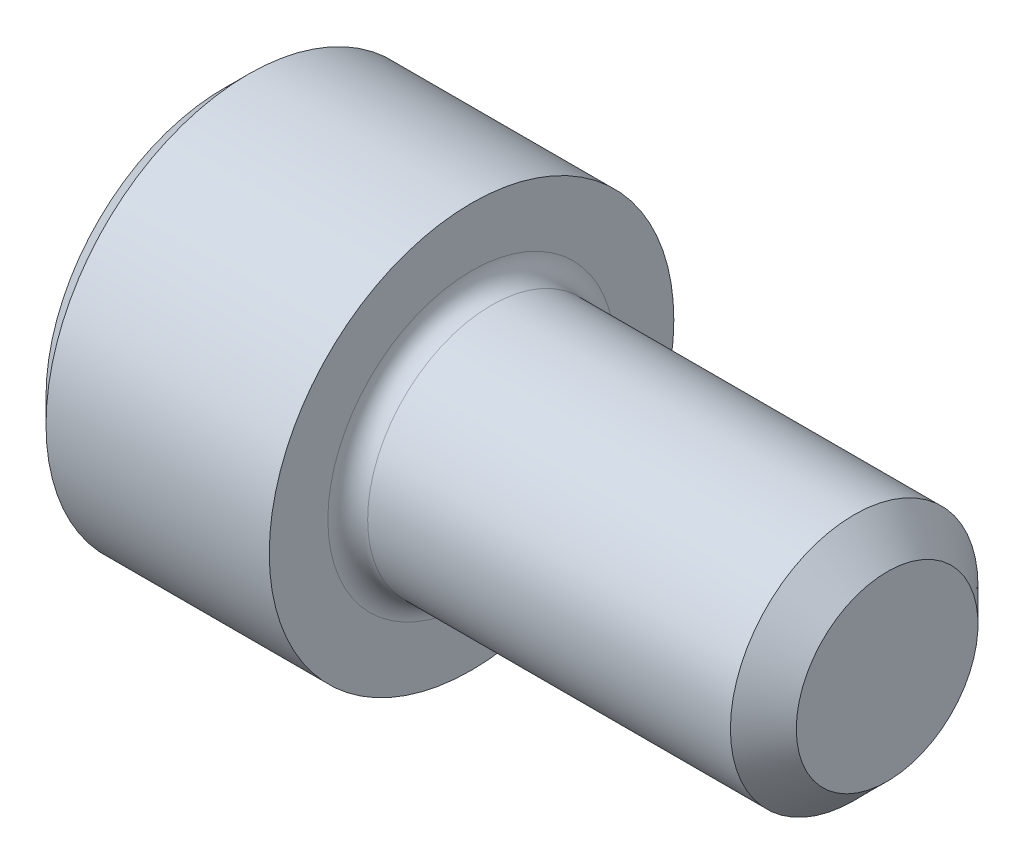
SolidWorks part; units mm, degrees
ref_plane "Plane1" through (0, 0, 0) normal (0, 0, 1) x (1, 0, 0)
ref_plane "Plane2" through (0, 0, 0) normal (0, 1, 0) x (1, 0, 0)
ref_plane "Plane3" through (0, 0, 0) normal (1, 0, 0) x (0, 0, -1)
sketch "BodySke" plane through (0, 0, 0) normal (0, 0, 1) x (1, 0, 0)
  line L0 (0, 0) -> (0, 2.0447)
  line L1 (0.2794, 2.3241) -> (2.8448, 2.3241)
  line L2 (2.8448, 2.3241) -> (2.8448, 1.4224)
  line L3 (2.8448, 1.4224) -> (7.2415, 1.4224)
  line L4 (7.62, 1.0439) -> (7.62, 0)
  line L5 (7.62, 0) -> (0, 0)
  line L6 (-31.75, 0) -> (127, 0) construction
  line L7 (0, 2.0447) -> (0.2794, 2.3241)
  line L8 (7.62, 1.0439) -> (7.2415, 1.4224)
  line L9 (0, -2.0447) -> (0.2794, -2.3241) construction
  line L10 (7.62, -1.0439) -> (7.2415, -1.4224) construction
  line L11 (3.4798, 9.525) -> (3.4798, 3.175) construction
  line L12 (2.8448, 9.525) -> (2.8448, 3.175) construction
  line L13 (-30.48, 9.525) -> (-30.48, 3.175) construction
  dimension "Diameter" = 2.8448
  dimension "Head_ht" = 2.8448
  dimension "Length" = 4.7752
  dimension "Body_ch_ang" = 45
  dimension "Head_dia" = 4.6482
  dimension "Head_ch_ang" = 45
  dimension "Head_side_ht" = 2.5654
  dimension "Minor_dia" = 2.0879
  dimension "Advance" = 0.635
  dimension "Thread_nom" = 4.7752
  dimension "Thread_length" = 38.1
revolve "Base-Revolve" add sketch "BodySke"
cosmetic thread "ThreadCosmetic" [suppressed]
fillet "Fillet1" radius 0.2286 1 edges at (2.8448, 0, 1.4224)
sketch "Sketch2" plane through (0, 0, 0) normal (0, 0, 1) x (1, 0, 0)
  line L0 (0, 1.1938) -> (1.2954, 1.1938)
  line L1 (1.2954, 1.1938) -> (1.9846, 0)
  line L2 (-31.75, 0) -> (127, 0) construction
  line L3 (1.9846, 0) -> (0, 0)
  line L4 (0, 0) -> (0, 1.1938)
  line L5 (0, 2.0447) -> (0, -2.0447) construction
  line L6 (0, 0) -> (47.625, 0) construction
  line L7 (2.8448, -2.3241) -> (2.8448, 2.3241) construction
  dimension "D1" = 1.1938
  dimension "D2" = 60
  dimension "Wall_thickness" = 1.5494
revolve "Hex-PreBroach" cut sketch "Sketch2" angle 360 about L6
sketch "Sketch3" plane through (0, 0, 0) normal (-1, 0, 0) x (0, 0.5, 0.866)
  line L0 (0.6892, 1.1938) -> (-0.6892, 1.1938)
  line L1 (-0.6892, 1.1938) -> (-1.3785, 0)
  line L2 (0.6892, 1.1938) -> (1.3785, 0)
  line L3 (0.6892, -1.1938) -> (1.3785, 0)
  line L4 (0.6892, -1.1938) -> (-0.6892, -1.1938)
  line L5 (-0.6892, -1.1938) -> (-1.3785, 0)
  dimension "D1" = 1.1938
  dimension "D2" = 1.1938
  dimension "Hex_size" = 2.3876
extrude "Hex" cut sketch "Sketch3" against normal blind 1.2954
sketch "Sketch4" plane through (0, 0, 0) normal (-1, 0, 0) x (0, 0, 1)
  line L0 (0, 0) -> (1.4605, 0)
  line L1 (0, 0) -> (6.1484, 3.5498) construction
  line L2 (0, 0) -> (0.7302, 1.2648)
  line L3 (1.2009, 0.3267) -> (1.3933, 0.4378)
  line L4 (0.8834, 0.8767) -> (1.0758, 0.9877)
  arc A0 (1.2009, 0.3267) -> (0.8834, 0.8767) centre (0, 0) ccw
  arc A1 (1.4605, 0) -> (1.3933, 0.4378) centre (0, 0) ccw
  arc A2 (0.7302, 1.2648) -> (1.0758, 0.9877) centre (0, 0) cw
  dimension "D1" = 30
  dimension "Spline_n_dim" = 2.4892
  dimension "Spline_m_dim" = 2.921
  dimension "D2" = 60
  dimension "D3" = 0.3175
  dimension "Spline_p_dim" = 0.635
extrude "Spline" [suppressed] cut sketch "Sketch4" against normal blind 1.2954
pattern_circular "CirPattern1" [suppressed] count 6 every 60
sketch "Sketch5" plane through (0, 0, 0) normal (0, 0, 1) x (1, 0, 0)
  line L0 (-31.75, 0) -> (127, 0) construction
  line L2 (0, 2.0447) -> (0, -2.0447) construction
  circle A0 centre (1.016, 0) radius 0.4445
  dimension "Drilled_hole_dia" = 0.889
  dimension "Drilled_hole_loc" = 1.016
extrude "Hole" [suppressed] cut sketch "Sketch5" against normal through all and the other way through all
pattern_circular "Drilled-4" [suppressed] count 2 every 60
pattern_circular "Drilled-6" [suppressed] count 3 every 60
sketch "ThdSchSke" plane through (0, 0, 0) normal (0, 0, 1) x (1, 0, 0)
  line L0 (3.4798, -1.0439) -> (3.2148, -1.4224)
  line L1 (3.4798, -1.0439) -> (3.7448, -1.4224)
  line L2 (3.7448, -1.4224) -> (3.7448, -1.778)
  line L3 (-3.175, 0) -> (5.1513, 0) construction
  line L5 (3.7448, -1.778) -> (3.2148, -1.778)
  line L6 (3.2148, -1.778) -> (3.2148, -1.4224)
  line L7 (0, 2.0447) -> (0, -2.0447) construction
  dimension "Thread_minor" = 2.0879
  dimension "Diameter" = 2.8448
  dimension "Start" = 3.4798
  dimension "SideAngle" = 55
  dimension "VeeAngle" = 70
  dimension "Overcut" = 3.556
revolve "ThreadSchematic" [suppressed] cut sketch "ThdSchSke" angle 360 about L3
pattern_linear "ThdSchPat" [suppressed]
equation "\"D2@Sketch3\" = \"Hex_size@Sketch3\" / 2"
equation "\"D1@Sketch3\" = \"Hex_size@Sketch3\" / 2"
equation "\"D1@Sketch2\" = \"Hex_size@Sketch3\" / 2"
equation "\"D3@Sketch4\" = \"Spline_p_dim@Sketch4\" / 2"
equation "\"Thread_minor@ThreadCosmetic\"  =  \"Minor_dia@BodySke\""
equation "\"D2@CirPattern1\" = 360 / \"Num_teeth@CirPattern1\""
equation "\"Wall_thickness@Sketch2\" = \"Head_ht@BodySke\" - \"Key_eng@Hex\""
equation "\"Thread_length@ThreadCosmetic\" = ((sgn( (\"Length@BodySke\" - \"Advance@BodySke\" ) - \"Thread_nom@BodySke\" )-1)*( (\"Length@BodySke\" - \"Advance@BodySke\" ) - \"Thread_nom@BodySke\" ))/-2+ \"Thread_nom@BodySke\""
equation "\"Thread_minor@ThdSchSke\" = \"Minor_dia@BodySke\""
equation "\"Diameter@ThdSchSke\" = \"Diameter@BodySke\""
equation "\"Overcut@ThdSchSke\" = \"Diameter@BodySke\" * 1.25"
equation "\"Start@ThdSchSke\" = \"Head_ht@BodySke\" + \"Length@BodySke\" - \"Thread_length@ThreadCosmetic\"  '---Non-countersunk---"
equation "\"Num_threads@ThdSchPat\" = int( \"Thread_length@ThreadCosmetic\" / \"Advance@BodySke\" + 0.999 )  + 1"
equation "\"Advance@ThdSchPat\" = \"Thread_length@ThreadCosmetic\" /  (\"Num_threads@ThdSchPat\" - 1) 'relax it"
equation "\"Num_threads@ThdSchPat\" = \"Num_threads@ThdSchPat\" - sgn( \"Num_threads@ThdSchPat\" - 1) '---chamfered tips only---"
